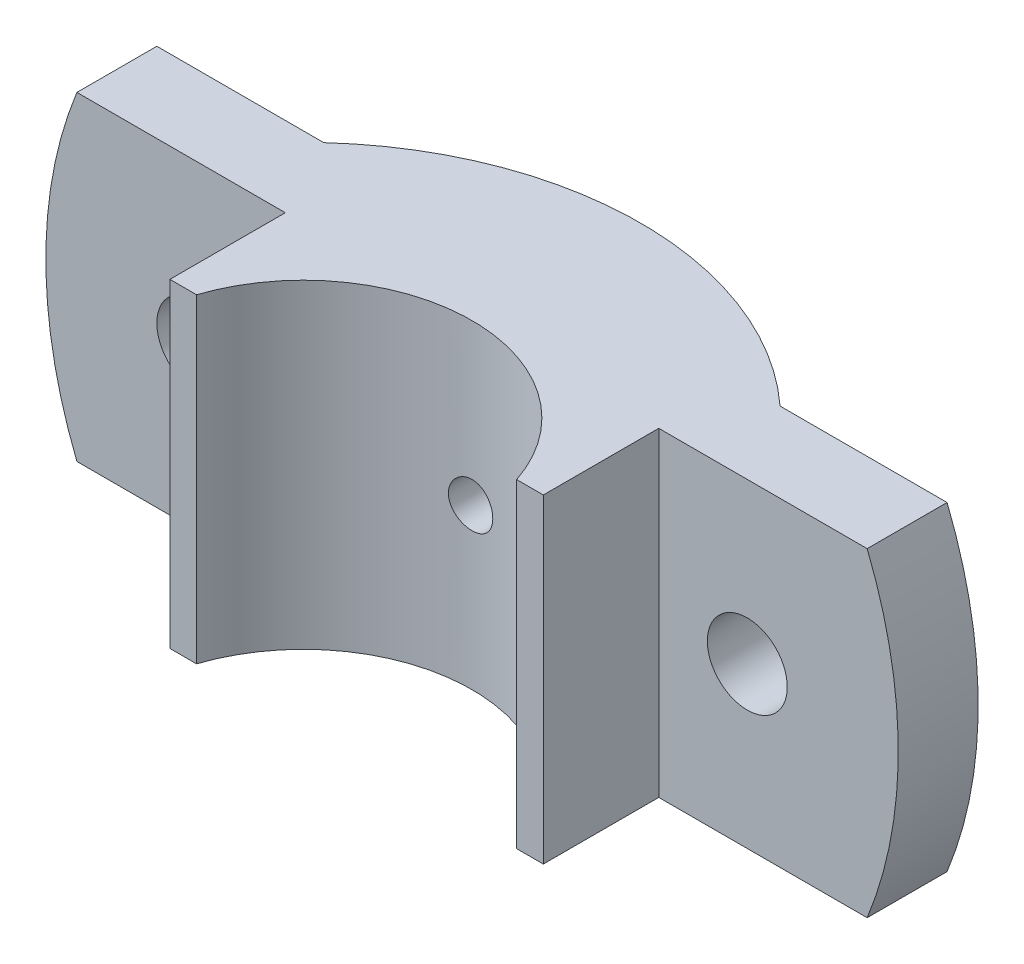
SolidWorks part; units mm, degrees
ref_plane "Front Plane" through (0, 0, 0) normal (0, 0, 1) x (1, 0, 0)
ref_plane "Top Plane" through (0, 0, 0) normal (0, 1, 0) x (1, 0, 0)
ref_plane "Right Plane" through (0, 0, 0) normal (1, 0, 0) x (0, 0, -1)
sketch "Sketch2" plane through (0, 0, 0) normal (0, 1, 0) x (1, 0, 0)
  line L0 (0, 0) -> (0, 93.1504) construction
  line L1 (-25.6905, 28) -> (-50, 28)
  line L2 (-50, 28) -> (-50, 19)
  line L3 (-50, 19) -> (-21.0278, 19)
  line L4 (-21.0278, 19) -> (-21.0278, 6)
  line L5 (-21.0278, 6) -> (-18.0278, 6)
  line L6 (21.0278, 6) -> (18.0278, 6)
  line L7 (21.0278, 19) -> (21.0278, 6)
  line L8 (50, 19) -> (21.0278, 19)
  line L9 (50, 28) -> (50, 19)
  line L10 (25.6905, 28) -> (50, 28)
  arc A0 (18.0278, 6) -> (-18.0278, 6) centre (0, 0) ccw
  arc A1 (25.6905, 28) -> (-25.6905, 28) centre (0, 0) ccw
  dimension "D1" = 19
  dimension "D5" = 38
  dimension "D2" = 3
  dimension "D3" = 13
  dimension "D4" = 6
  dimension "D6" = 9
  dimension "D7" = 50
extrude "Boss-Extrude1" add sketch "Sketch2" along normal mid plane 36
sketch "Sketch4" plane through (0, 0, -28) normal (0, 0, -1) x (-1, 0, 0)
  line L4 (-50, -18) -> (-25.6905, -18)
  line L5 (-25.6905, -18) -> (-25.6905, 18)
  line L6 (-25.6905, 18) -> (-50, 18)
  line L7 (-50, 18) -> (-50, -18)
  line L8 (-50, -18) -> (-44.4972, -18)
  line L10 (-44.4972, 18) -> (-50, 18)
  line L11 (-50, 18) -> (-50, -18)
  arc A0 (-44.4972, 18) -> (-44.4972, -18) centre (0, 0) ccw
  dimension "D1" = 0
extrude "Cut-Extrude1" cut sketch "Sketch4" against normal blind 36
mirror "Mirror1" about plane through (0, 0, 0) normal (1, 0, 0) of "Cut-Extrude1"
sketch "Sketch7" plane through (0, 0, -28) normal (0, 0, -1) x (-1, 0, 0)
  line L0 (-44.4972, -18) -> (-25.6905, -18) construction
  circle A0 centre (-31, 0) radius 4.5
  dimension "D1" = 31
  dimension "D3" = 9
  dimension "D2" = 18
extrude "Cut-Extrude3" cut sketch "Sketch7" against normal blind 36
sketch "Sketch8" plane through (0, 0, -28) normal (0, 0, -1) x (-1, 0, 0)
  line L0 (-25.6905, 18) -> (-25.6905, -18) construction
  line L1 (-25.6905, 6.6377) -> (-25.6905, -6.6377)
  arc A0 (-25.6905, 6.6377) -> (-25.6905, -6.6377) centre (-31, 0) cw
  dimension "D1" = 8.5
extrude "Cut-Extrude4" cut sketch "Sketch8" along normal through all
mirror "Mirror3" about plane through (0, 0, 0) normal (1, 0, 0) of "Cut-Extrude4", "Cut-Extrude3"
hole_wizard "CBORE for M5 Hex Head Bolt1" positions "3DSketch2" profile "Sketch11" counterbore size "M5" standard "ANSI Metric" end condition through all
sketch3d "3DSketch2"
  point P0 (0, 0, -38)
  dimension "D1" = 0
  dimension "D2" = 0
sketch "Sketch11" plane through (0, 0, -38) normal (1, 0, 0) x (0, 1, 0)
  line L0 (0, 0) -> (0, 32)
  line L1 (0, 32) -> (2.5, 32)
  line L2 (2.5, 13.3001) -> (2.5, 32)
  line L3 (2.5, 13.3001) -> (2.9995, 13)
  line L4 (2.9995, 13) -> (3, 13)
  line L5 (3, 13) -> (3, 0)
  line L7 (0, 0) -> (3, 0)
  line L9 (-2.5, 13.3001) -> (-2.9995, 13) construction
  line L11 (0, -6.35) -> (0, 107.95) construction
  dimension "Thru Hole Dia." = 5
  dimension "Thru Hole Depth" = 32
  dimension "C'Bore Dia." = 6
  dimension "C'Bore Depth" = 13
  dimension "Mid C'Sink Dia." = 5.999
  dimension "Mid C'Sink Angle" = 118
